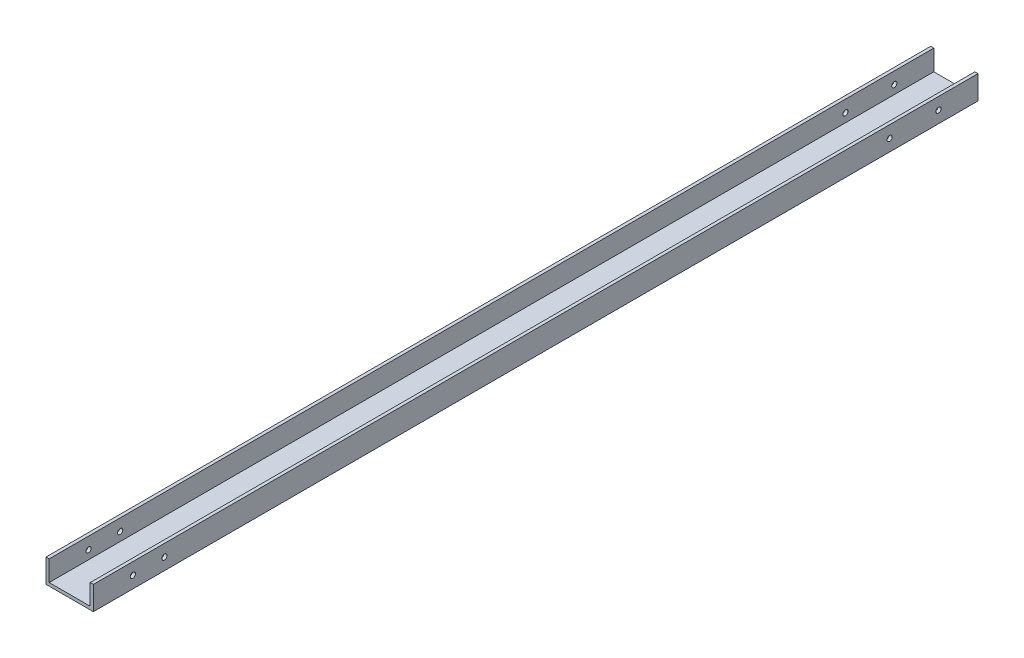
SolidWorks part; units mm, degrees
ref_plane "正面" through (0, 0, 0) normal (0, 0, 1) x (1, 0, 0)
ref_plane "平面" through (0, 0, 0) normal (0, 1, 0) x (1, 0, 0)
ref_plane "右側面" through (0, 0, 0) normal (1, 0, 0) x (0, 0, -1)
sketch "ｽｹｯﾁ1" plane through (0, 0, 0) normal (0, 0, 1) x (1, 0, 0)
  line L0 (0, 0) -> (15, 0)
  line L1 (0, 0) -> (-15, 0)
  line L2 (-15, 0) -> (-15, 15)
  line L3 (15, 0) -> (15, 15)
  line L4 (-15, 15) -> (-13, 15)
  line L5 (15, 15) -> (13, 15)
  line L6 (-13, 15) -> (-13, 2)
  line L7 (13, 15) -> (13, 2)
  line L8 (-13, 2) -> (13, 2)
  dimension "D1" = 15
  dimension "D2" = 15
  dimension "D3" = 15
  dimension "D4" = 15
  dimension "D5" = 2
  dimension "D6" = 2
  dimension "D7" = 13
  dimension "D8" = 13
extrude "ﾎﾞｽ - 押し出し1" add sketch "ｽｹｯﾁ1" along normal blind 560.3
sketch "ｽｹｯﾁ4" plane through (15, 0, 0) normal (1, 0, 0) x (0, 0, -1)
  line L0 (-560.3, 7.5) -> (-535.3, 7.5)
  line L1 (-560.3, 0) -> (-560.3, 15) construction
  line L2 (-560.3, 7.5) -> (-515.3, 7.5)
  circle A0 centre (-535.3, 7.5) radius 2.2
  circle A1 centre (-515.3, 7.5) radius 2.2
  dimension "D3" = 4.4
  dimension "D4" = 4.4
  dimension "D1" = 25
  dimension "D2" = 45
sketch "ｽｹｯﾁ5" plane through (15, 0, 0) normal (1, 0, 0) x (0, 0, -1)
  line L0 (0, 7.5) -> (-25, 7.5)
  line L1 (0, 0) -> (0, 15) construction
  line L2 (0, 7.5) -> (-56, 7.5)
  circle A0 centre (-25, 7.5) radius 2.2
  circle A1 centre (-56, 7.5) radius 2.2
  dimension "D3" = 4.4
  dimension "D4" = 4.4
  dimension "D1" = 25
  dimension "D2" = 56
sketch "ｽｹｯﾁ7" plane through (-15, 0, 0) normal (-1, 0, 0) x (0, 0, 1)
  line L1 (535.3, 7.5) -> (515.3, 7.5)
  line L2 (535.3, 7.5) -> (560.3, 7.5)
  line L3 (25, 7.5) -> (0, 7.5)
  line L4 (25, 7.5) -> (56, 7.5)
  circle A0 centre (25, 7.5) radius 2.2
  circle A1 centre (56, 7.5) radius 2.2
  circle A2 centre (515.3, 7.5) radius 2.2
  circle A3 centre (535.3, 7.5) radius 2.2
  dimension "D1" = 4.4
  dimension "D2" = 4.4
  dimension "D3" = 25
  dimension "D4" = 20
  dimension "D5" = 25
  dimension "D6" = 31
sketch "ｽｹｯﾁ8" plane through (15, 0, 0) normal (1, 0, 0) x (0, 0, -1)
  line L0 (0, 7.5) -> (-25, 7.5)
  line L1 (-25, 7.5) -> (-56, 7.5)
  circle A0 centre (-56, 7.5) radius 2.5943
  circle A1 centre (-25, 7.5) radius 2.9358
  dimension "D1" = 25
  dimension "D2" = 31
hole_wizard "M4x0.7 ねじ穴1" positions "3Dｽｹｯﾁ1" profile "ｽｹｯﾁ9" tap size "M4x0.7" standard "JIS"
sketch3d "3Dｽｹｯﾁ1"
  point P0 (15, 7.5, 56)
  point P3 (15, 7.5, 25)
sketch "ｽｹｯﾁ9" plane through (15, 7.5, 56) normal (0, 1, 0) x (0, 0, -1)
  line L0 (0, 0) -> (0, 12.4914)
  line L1 (0, 12.4914) -> (1.65, 11.5)
  line L2 (1.65, 11.5) -> (1.65, 0)
  line L5 (1.65, 0) -> (0, 0)
  line L10 (0, 12.4914) -> (-1.65, 11.5) construction
  line L11 (0, -6.35) -> (0, 107.95) construction
  dimension "ねじ下穴ﾄﾞﾘﾙ直径" = 3.3
  dimension "ねじ下穴ﾄﾞﾘﾙの深さ" = 11.5
  dimension "ﾄﾞﾘﾙ角度" = 118
cosmetic thread "穴のねじ山1"
cosmetic thread "穴のねじ山2"
hole_wizard "M4x0.7 ねじ穴2" positions "3Dｽｹｯﾁ2" profile "ｽｹｯﾁ10" tap size "M4x0.7" standard "JIS"
sketch3d "3Dｽｹｯﾁ2"
  point P0 (15, 7.5, 535.3)
  point P3 (15, 7.5, 515.3)
sketch "ｽｹｯﾁ10" plane through (15, 7.5, 535.3) normal (0, 1, 0) x (0, 0, -1)
  line L0 (0, 0) -> (0, 12.4914)
  line L1 (0, 12.4914) -> (1.65, 11.5)
  line L2 (1.65, 11.5) -> (1.65, 0)
  line L5 (1.65, 0) -> (0, 0)
  line L10 (0, 12.4914) -> (-1.65, 11.5) construction
  line L11 (0, -6.35) -> (0, 107.95) construction
  dimension "ねじ下穴ﾄﾞﾘﾙ直径" = 3.3
  dimension "ねじ下穴ﾄﾞﾘﾙの深さ" = 11.5
  dimension "ﾄﾞﾘﾙ角度" = 118
cosmetic thread "穴のねじ山3"
cosmetic thread "穴のねじ山4"
hole_wizard "M4x0.7 ねじ穴4" positions "3Dｽｹｯﾁ4" profile "ｽｹｯﾁ12" tap size "M4x0.7" standard "JIS"
sketch3d "3Dｽｹｯﾁ4"
  point P0 (-15, 7.5, 56)
  point P3 (-15, 7.5, 25)
  point P6 (-15, 7.5, 515.3)
  point P9 (-15, 7.5, 535.3)
sketch "ｽｹｯﾁ12" plane through (-15, 7.5, 56) normal (0, 1, 0) x (0, 0, 1)
  line L0 (0, 0) -> (0, 12.4914)
  line L1 (0, 12.4914) -> (1.65, 11.5)
  line L2 (1.65, 11.5) -> (1.65, 0)
  line L5 (1.65, 0) -> (0, 0)
  line L10 (0, 12.4914) -> (-1.65, 11.5) construction
  line L11 (0, -6.35) -> (0, 107.95) construction
  dimension "ねじ下穴ﾄﾞﾘﾙ直径" = 3.3
  dimension "ねじ下穴ﾄﾞﾘﾙの深さ" = 11.5
  dimension "ﾄﾞﾘﾙ角度" = 118
cosmetic thread "穴のねじ山9"
cosmetic thread "穴のねじ山10"
cosmetic thread "穴のねじ山11"
cosmetic thread "穴のねじ山12"
sketch "ｽｹｯﾁ14" plane through (0, 0, 0) normal (0, -1, 0) x (-1, 0, 0)
  line L0 (15, -560.3) -> (15, -515.3)
  line L1 (15, -560.3) -> (15, 0) construction
  line L2 (15, -515.3) -> (-11, -515.3)
  line L3 (-11, -515.3) -> (-11, -525.6)
  line L4 (-11, -525.6) -> (11.2, -525.6)
  line L5 (11.2, -525.6) -> (11.2, -515.3)
  circle A0 centre (-11, -525.6) radius 1.6
  circle A2 centre (11.2, -515.3) radius 1.6
  dimension "D5" = 3.2
  dimension "D6" = 3.2
  dimension "D1" = 45
  dimension "D2" = 26
  dimension "D3" = 10.3
  dimension "D4" = 22.2
